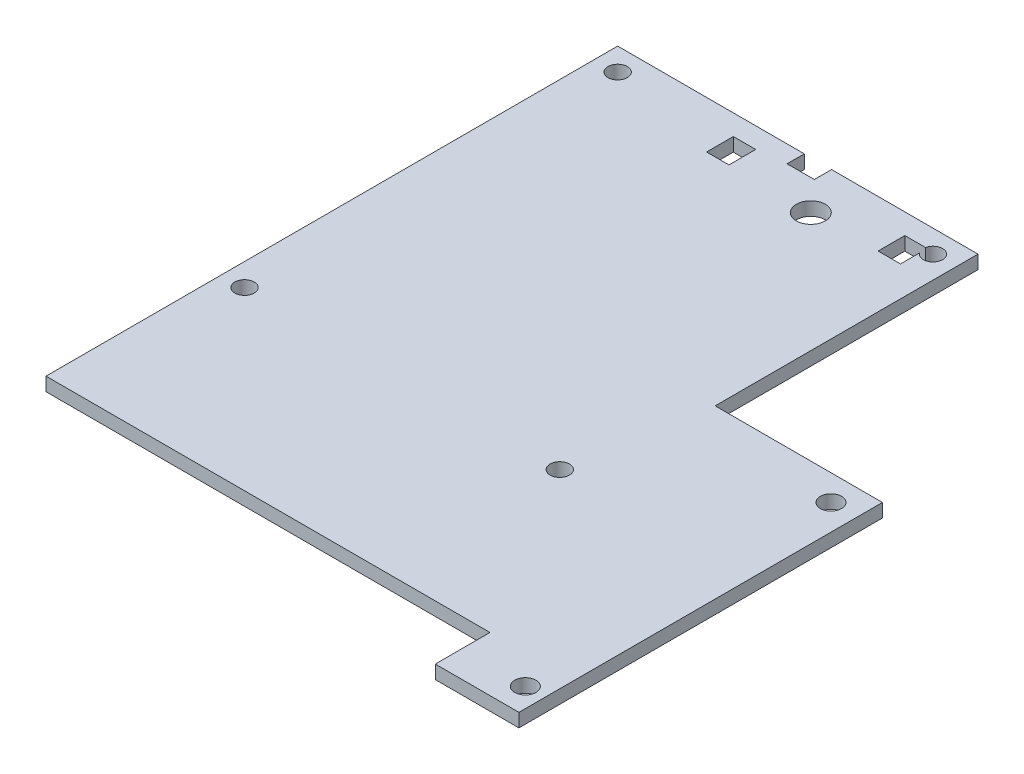
SolidWorks part; units mm, degrees
ref_plane "Front Plane" through (0, 0, 0) normal (0, 0, 1) x (1, 0, 0)
ref_plane "Top Plane" through (0, 0, 0) normal (0, 1, 0) x (1, 0, 0)
ref_plane "Right Plane" through (0, 0, 0) normal (1, 0, 0) x (0, 0, -1)
sketch "Sketch1" plane through (0, 0, 0) normal (0, 1, 0) x (1, 0, 0)
  line L0 (0, 0) -> (0, 88.85)
  line L1 (0, 88.85) -> (56, 88.85)
  line L2 (56, 88.85) -> (56, 48)
  line L3 (56, 48) -> (82, 48)
  line L4 (82, 48) -> (82, -8.5)
  line L5 (82, -8.5) -> (69, -8.5)
  line L6 (69, -8.5) -> (69, 0)
  line L7 (69, 0) -> (0, 0)
  line L9 (21.16, 85.66) -> (24.64, 85.66)
  line L10 (21.16, 85.66) -> (21.16, 81.5)
  line L11 (21.16, 81.5) -> (24.64, 81.5)
  line L12 (24.64, 85.66) -> (24.64, 81.5)
  line L13 (51.3, 81.5) -> (47.82, 81.5)
  line L14 (51.3, 81.5) -> (51.3, 85.66)
  line L15 (51.3, 85.66) -> (47.82, 85.66)
  line L16 (47.82, 81.5) -> (47.82, 85.66)
  line L17 (29.01, 88.85) -> (33.24, 88.85)
  line L18 (29.01, 88.85) -> (29.01, 86.17)
  line L19 (29.01, 86.17) -> (33.24, 86.17)
  line L20 (33.24, 88.85) -> (33.24, 86.17)
  circle A0 centre (3.5, 85.35) radius 1.5
  circle A1 centre (52.5, 85.35) radius 1.5
  circle A2 centre (37.42, 81.45) radius 2.25
  circle A3 centre (3.5, 27.35) radius 1.5
  circle A4 centre (52.5, 27.35) radius 1.5
  circle A5 centre (78, 44) radius 1.65
  circle A6 centre (79, -4.5) radius 1.65
  dimension "D6" = 3
  dimension "D9" = 3
  dimension "D11" = 4.5
  dimension "D14" = 3
  dimension "D16" = 3
  dimension "D17" = 3.3
  dimension "D25" = 3.3
  dimension "D1" = 56
  dimension "D2" = 26
  dimension "D3" = 56.5
  dimension "D4" = 8.5
  dimension "D5" = 13
  dimension "D7" = 3.5
  dimension "D8" = 3.5
  dimension "D10" = 3.5
  dimension "D12" = 7.4
  dimension "D13" = 18.58
  dimension "D15" = 58
  dimension "D18" = 22
  dimension "D19" = 44.85
  dimension "D20" = 4
  dimension "D21" = 3.5
  dimension "D22" = 49
  dimension "D23" = 58
  dimension "D24" = 3.5
  dimension "D26" = 48.5
  dimension "D27" = 23
  dimension "D28" = 3.48
  dimension "D29" = 4.16
  dimension "D30" = 3.19
  dimension "D31" = 31.36
  dimension "D32" = 4.7
  dimension "D33" = 3.48
  dimension "D34" = 4.16
  dimension "D35" = 3.19
  dimension "D36" = 2.68
  dimension "D37" = 4.23
  dimension "D38" = 22.76
extrude "Boss-Extrude2" add sketch "Sketch1" against normal blind 2.1 contours L7 L6 L5 L4 L3 L2 L1 L0 A6 A5 A4 A3 A2 A1 L14 L13 L16 L15 A0 L9 L12 L11 L10
sketch "Sketch3" plane through (0, 0, 0) normal (0, 1, 0) x (1, 0, 0)
  line L0 (0, 88.85) -> (0, 0)
  line L1 (0, 0) -> (69, 0)
  line L2 (69, 0) -> (69, -8.5)
  line L3 (69, -8.5) -> (69, 0) construction
  line L4 (69, -8.5) -> (82, -8.5)
  line L5 (82, -8.5) -> (82, 48)
  line L6 (82, 48) -> (56, 48)
  line L7 (56, 88.85) -> (56, 48) construction
  line L8 (56, 48) -> (82, 48) construction
  line L9 (56, 48) -> (56, 88.85)
  line L10 (56, 88.85) -> (51.3, 88.85)
  line L11 (33.24, 88.85) -> (56, 88.85) construction
  line L12 (51.3, 88.85) -> (51.3, 81.5)
  line L13 (51.3, 81.5) -> (47.82, 81.5)
  line L14 (47.82, 81.5) -> (47.82, 88.85)
  line L15 (47.82, 88.85) -> (33.24, 88.85)
  line L16 (33.24, 88.85) -> (33.24, 86.17)
  line L17 (33.24, 86.17) -> (29.01, 86.17)
  line L18 (29.01, 86.17) -> (29.01, 88.85)
  line L19 (29.01, 88.85) -> (24.64, 88.85)
  line L20 (0, 88.85) -> (29.01, 88.85) construction
  line L21 (24.64, 88.85) -> (24.64, 81.5)
  line L22 (24.64, 81.5) -> (21.16, 81.5)
  line L23 (21.16, 81.5) -> (21.16, 88.85)
  line L24 (21.16, 88.85) -> (0, 88.85)
